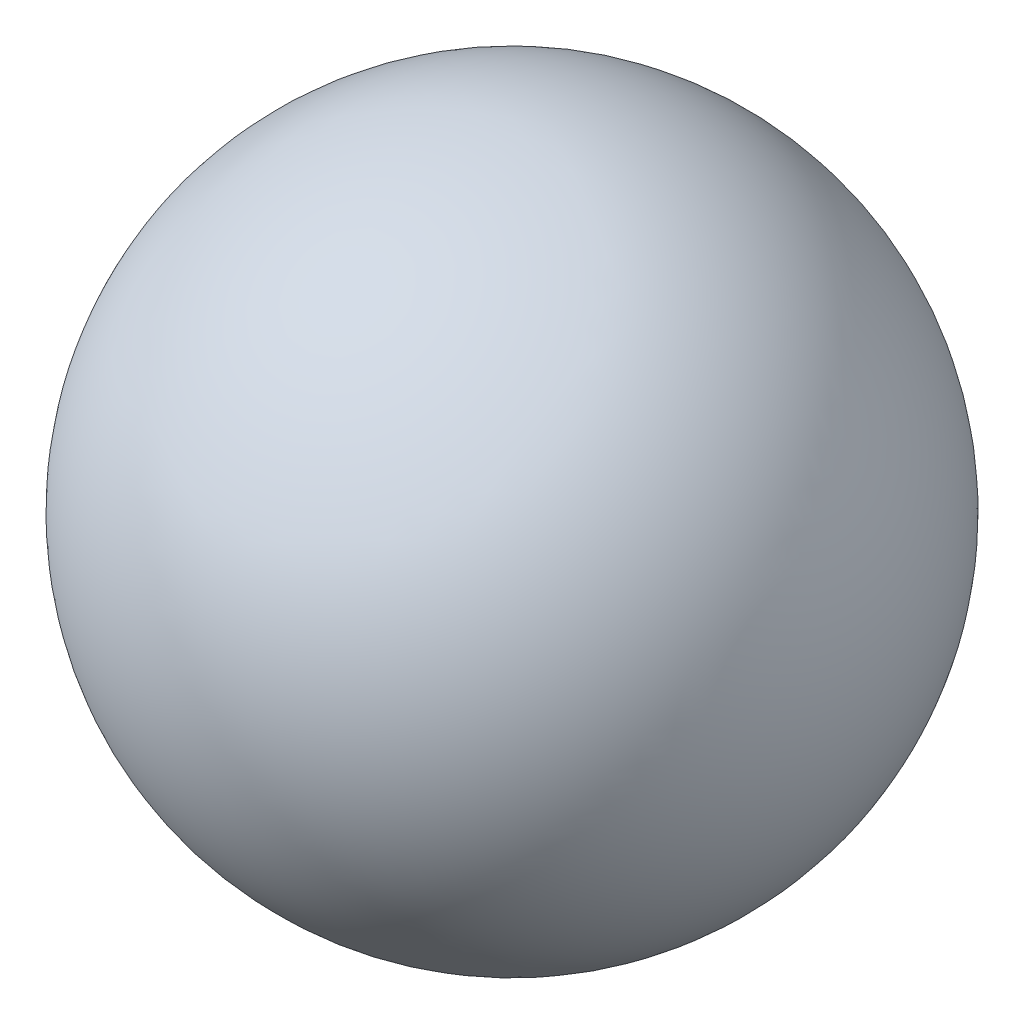
SolidWorks part; units mm, degrees
ref_plane "Front Plane" through (0, 0, 0) normal (0, 0, 1) x (1, 0, 0)
ref_plane "Top Plane" through (0, 0, 0) normal (0, 1, 0) x (1, 0, 0)
ref_plane "Right Plane" through (0, 0, 0) normal (1, 0, 0) x (0, 0, -1)
sketch "Sketch1" plane through (0, 0, 0) normal (0, 1, 0) x (1, 0, 0)
  line L0 (-3.2, 0) -> (3.2, 0)
  arc A0 (-3.2, 0) -> (3.2, 0) centre (0, 0) cw
  point P3 (0, 0)
  dimension "D1" = 3.2
revolve "Revolve1" add sketch "Sketch1" angle 360 about L0
